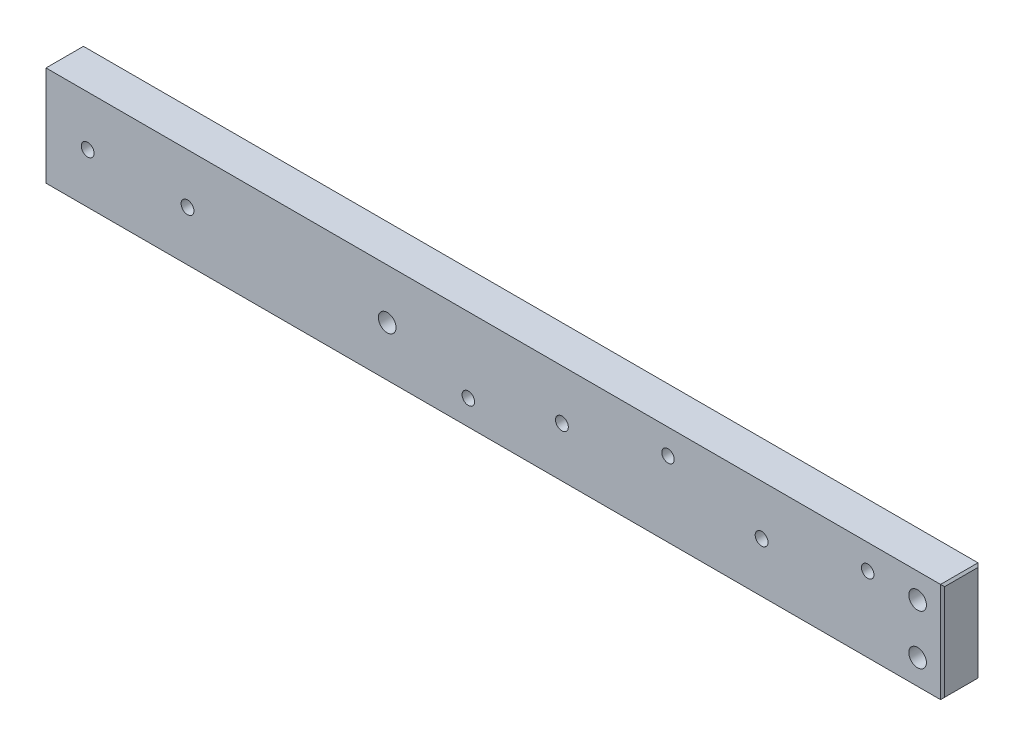
SolidWorks part; units mm, degrees
material "6061-T6 (SS)"
ref_plane "Front Plane" through (0, 0, 0) normal (0, 0, 1) x (1, 0, 0)
ref_plane "Top Plane" through (0, 0, 0) normal (0, 1, 0) x (1, 0, 0)
ref_plane "Right Plane" through (0, 0, 0) normal (1, 0, 0) x (0, 0, -1)
sketch "Sketch1" plane through (0, 0, 0) normal (0, 0, 1) x (1, 0, 0)
  line L1 (0, 0) -> (-228.6, 0)
  line L2 (0, 0) -> (0, 25.4)
  line L3 (0, 25.4) -> (-228.6, 25.4)
  line L4 (-228.6, 0) -> (-228.6, 25.4)
  dimension "D1" = 25.4
  dimension "D2" = 228.6
extrude "Boss-Extrude1" add sketch "Sketch1" along normal blind 9.525
sketch "Sketch2" plane through (0, 0, 9.525) normal (0, 0, 1) x (1, 0, 0)
  line L0 (-6.35, 6.35) -> (-6.35, 19.05)
  line L1 (-6.35, 19.05) -> (-6.35, 25.4)
  line L2 (0, 25.4) -> (-228.6, 25.4) construction
  line L3 (-6.35, 6.35) -> (-6.35, 0)
  line L4 (-228.6, 0) -> (0, 0) construction
  line L5 (0, 0) -> (0, 25.4) construction
  dimension "D1" = 6.35
  dimension "D2" = 12.7
hole_wizard "#8 Clearance Hole1" positions "Sketch3" profile "Sketch4" hole size "#8" standard "ANSI Inch"
sketch "Sketch3" plane through (0, 0, 9.525) normal (0, 0, 1) x (1, 0, 0)
  point P0 (-6.35, 6.35)
  point P3 (-6.35, 19.05)
sketch "Sketch4" plane through (-6.35, 6.35, 9.525) normal (1, 0, 0) x (0, -1, 0)
  line L0 (0, 0) -> (0, 26.7507)
  line L1 (0, 26.7507) -> (2.2479, 25.4)
  line L2 (2.2479, 25.4) -> (2.2479, 0)
  line L5 (2.2479, 0) -> (0, 0)
  line L10 (0, 26.7507) -> (-2.2479, 25.4) construction
  line L11 (0, -6.35) -> (0, 107.95) construction
  dimension "Hole Dia." = 4.4958
  dimension "Hole Depth" = 25.4
  dimension "Drill Angle" = 118
hole_wizard "#8 Clearance Hole2" positions "Sketch8" profile "Sketch9" hole size "#8" standard "ANSI Inch"
sketch "Sketch8" plane through (0, 0, 9.525) normal (0, 0, 1) x (1, 0, 0)
  line L0 (-204.7875, 12.7) -> (-141.2875, 12.7)
  line L1 (-204.7875, 12.7) -> (-228.6, 12.7)
  line L2 (-228.6, 25.4) -> (-228.6, 0) construction
  point P2 (-141.2875, 12.7)
  dimension "D1" = 63.5
  dimension "D2" = 23.8125
sketch "Sketch9" plane through (-141.2875, 12.7, 9.525) normal (1, 0, 0) x (0, -1, 0)
  line L0 (0, 0) -> (0, 20.4007)
  line L1 (0, 20.4007) -> (2.2479, 19.05)
  line L2 (2.2479, 19.05) -> (2.2479, 0)
  line L5 (2.2479, 0) -> (0, 0)
  line L10 (0, 20.4007) -> (-2.2479, 19.05) construction
  line L11 (0, -6.35) -> (0, 107.95) construction
  dimension "Hole Dia." = 4.4958
  dimension "Hole Depth" = 19.05
  dimension "Drill Angle" = 118
chamfer "Chamfer1" distance 0.508 angle 45 8 edges at (0, 0, 4.7625) (0, 12.7, 9.525) (0, 25.4, 4.7625) (0, 12.7, 0) (-228.6, 25.4, 4.7625) (-228.6, 12.7, 9.525) (-228.6, 0, 4.7625) (-228.6, 12.7, 0)
hole_wizard "#4 Clearance Hole1" positions "Sketch10" profile "Sketch12" hole size "#4" standard "ANSI Inch" end condition through all
sketch "Sketch10" plane through (0, 0, 0) normal (0, 0, -1) x (-1, 0, 0)
  point P0 (96.8375, 12.7)
  point P3 (46.0375, 12.7)
sketch "Sketch12" plane through (-96.8375, 12.7, 0) normal (1, 0, 0) x (0, 1, 0)
  line L0 (0, 0) -> (0, 9.525)
  line L1 (0, 9.525) -> (1.6319, 9.525)
  line L2 (1.6319, 9.525) -> (1.6319, 0)
  line L5 (1.6319, 0) -> (0, 0)
  line L11 (0, -6.35) -> (0, 107.95) construction
  dimension "Thru Hole Dia." = 3.2639
  dimension "Thru Hole Depth" = 9.525
hole_wizard "#4 Clearance Hole2" positions "Sketch13" profile "Sketch14" hole size "#4" standard "ANSI Inch" end condition up to next
sketch "Sketch13" plane through (0, 0, 9.525) normal (0, 0, 1) x (1, 0, 0)
  line L0 (-217.4875, 12.7) -> (-192.0875, 12.7)
  line L2 (-228.092, 25.4) -> (-228.092, 0) construction
  line L3 (-141.2875, 12.7) -> (-204.7875, 12.7) construction
  point P0 (-217.4875, 12.7)
  point P2 (-192.0875, 12.7)
  point P11 (-228.092, 12.7)
  dimension "D1" = 25.4
  dimension "D2" = 63.5
sketch "Sketch14" plane through (-217.4875, 12.7, 9.525) normal (1, 0, 0) x (0, -1, 0)
  line L0 (0, 0) -> (0, 9.525)
  line L1 (0, 9.525) -> (1.6319, 9.525)
  line L2 (1.6319, 9.525) -> (1.6319, 0)
  line L5 (1.6319, 0) -> (0, 0)
  line L11 (0, -6.35) -> (0, 107.95) construction
  dimension "Thru Hole Dia." = 3.2639
  dimension "Thru Hole Depth" = 9.525
hole_wizard "1/8 (0.125) Diameter Hole1" positions "Sketch15" profile "Sketch17" hole size "1/8" standard "ANSI Inch" end condition up to next
sketch "Sketch15" plane through (0, 0, 9.525) normal (0, 0, 1) x (1, 0, 0)
  line L1 (0, 24.892) -> (0, 0.508) construction
  line L2 (-69.85, 19.05) -> (-19.05, 19.05)
  line L5 (-0.508, 25.4) -> (-228.092, 25.4) construction
  line L6 (-228.092, 0) -> (-0.508, 0) construction
  point P0 (-19.05, 19.05)
  point P2 (-69.85, 19.05)
  point P22 (-120.65, 6.35)
  dimension "D1" = 69.85
  dimension "D2" = 19.05
  dimension "D3" = 6.35
  dimension "D4" = 6.35
  dimension "D5" = 120.65
sketch "Sketch17" plane through (-19.05, 19.05, 9.525) normal (1, 0, 0) x (0, -1, 0)
  line L0 (0, 0) -> (0, 9.525)
  line L1 (0, 9.525) -> (1.5875, 9.525)
  line L2 (1.5875, 9.525) -> (1.5875, 0)
  line L5 (1.5875, 0) -> (0, 0)
  line L11 (0, -6.35) -> (0, 107.95) construction
  dimension "Thru Hole Dia." = 3.175
  dimension "Thru Hole Depth" = 9.525
